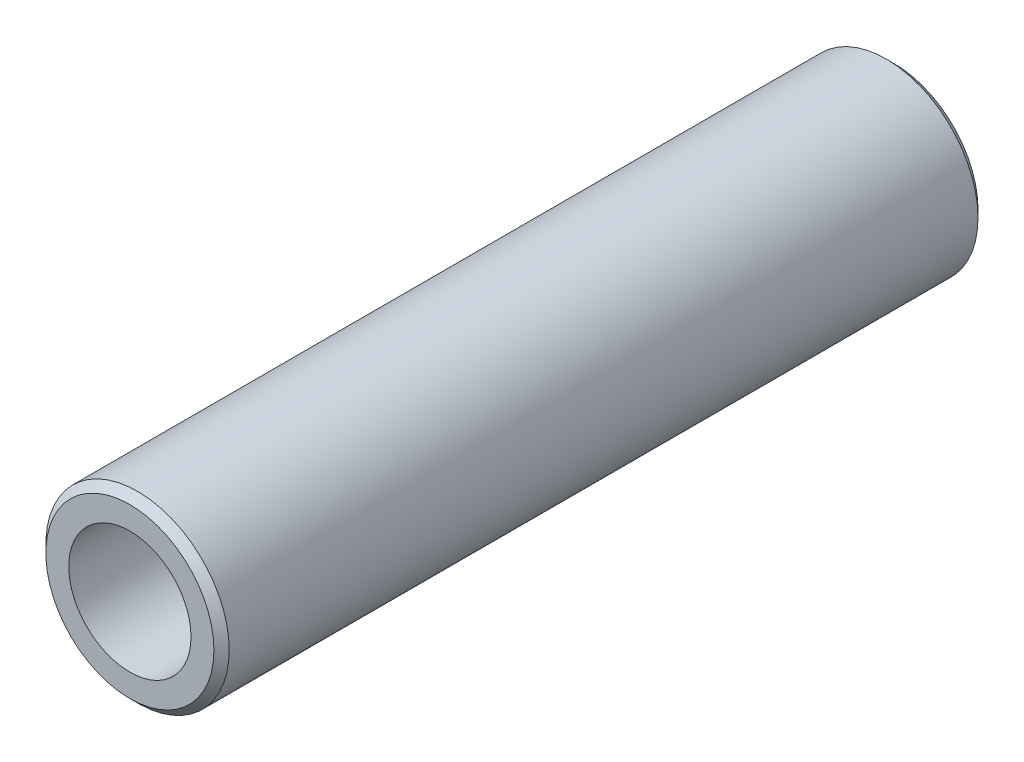
SolidWorks part; units mm, degrees
material "1060 Alloy"
ref_plane "Front Plane" through (0, 0, 0) normal (0, 0, 1) x (1, 0, 0)
ref_plane "Top Plane" through (0, 0, 0) normal (0, 1, 0) x (1, 0, 0)
ref_plane "Right Plane" through (0, 0, 0) normal (1, 0, 0) x (0, 0, -1)
sketch "Sketch1" plane through (0, 0, 0) normal (0, 0, 1) x (1, 0, 0)
  circle A0 centre (0, 0) radius 3
  circle A1 centre (0, 0) radius 2
  dimension "D1" = 6
  dimension "D2" = 4
extrude "Boss-Extrude1" add sketch "Sketch1" along normal mid plane 25
cosmetic thread "Cosmetic Thread1" parameters "D2"=5
chamfer "Chamfer1" distance 0.25 angle 45 2 edges at (3, 0, -12.5) (3, 0, 12.5)
